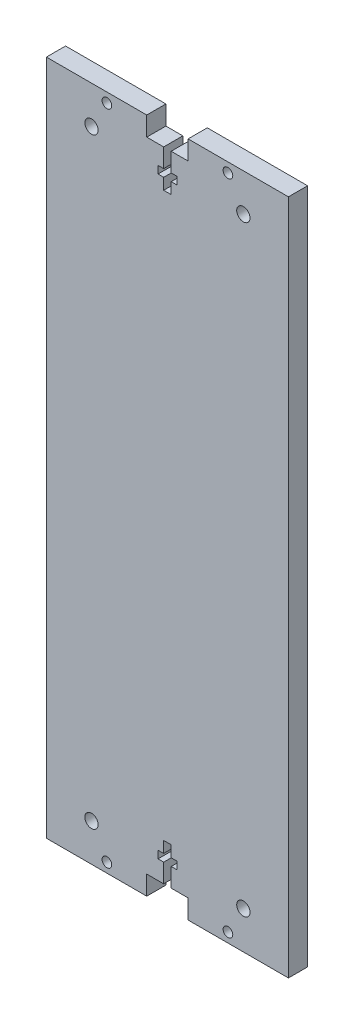
SolidWorks part; units mm, degrees
ref_plane "Front Plane" through (0, 0, 0) normal (0, 0, 1) x (1, 0, 0)
ref_plane "Top Plane" through (0, 0, 0) normal (0, 1, 0) x (1, 0, 0)
ref_plane "Right Plane" through (0, 0, 0) normal (1, 0, 0) x (0, 0, -1)
sketch "Sketch1" plane through (0, 0, 0) normal (0, 0, 1) x (1, 0, 0)
  line L0 (0, -107.823) -> (0, -114.3)
  line L1 (-40.894, -114.3) -> (40.894, -114.3)
  line L2 (-40.894, -114.3) -> (-40.894, 114.3)
  line L3 (-40.894, 114.3) -> (40.894, 114.3)
  line L4 (40.894, -114.3) -> (40.894, 114.3)
  line L5 (-40.894, -114.3) -> (40.894, 114.3) construction
  line L6 (-40.894, 114.3) -> (40.894, -114.3) construction
  line L7 (-6.985, -114.3) -> (6.985, -114.3)
  line L8 (-6.985, -114.3) -> (-6.985, -107.823)
  line L9 (-6.985, -107.823) -> (6.985, -107.823)
  line L10 (6.985, -114.3) -> (6.985, -107.823)
  line L11 (0, -95.123) -> (0, -107.823) construction
  line L12 (-1.27, -107.823) -> (1.27, -107.823)
  line L13 (-1.27, -107.823) -> (-1.27, -95.123)
  line L14 (-1.27, -95.123) -> (1.27, -95.123)
  line L15 (1.27, -107.823) -> (1.27, -95.123)
  line L16 (0, -98.933) -> (0, -101.473) construction
  line L17 (-3.175, -101.473) -> (3.175, -101.473)
  line L18 (-3.175, -101.473) -> (-3.175, -98.933)
  line L19 (-3.175, -98.933) -> (3.175, -98.933)
  line L20 (3.175, -101.473) -> (3.175, -98.933)
  line L21 (0, 0) -> (-40.894, 0) construction
  line L22 (0, 98.933) -> (0, 101.473) construction
  line L23 (0, 95.123) -> (0, 107.823) construction
  line L24 (3.175, 101.473) -> (3.175, 98.933)
  line L25 (-3.175, 98.933) -> (3.175, 98.933)
  line L26 (-3.175, 101.473) -> (-3.175, 98.933)
  line L27 (-3.175, 101.473) -> (3.175, 101.473)
  line L28 (0, 0) -> (0, 14.3328) construction
  line L29 (1.27, 107.823) -> (1.27, 95.123)
  line L30 (-1.27, 95.123) -> (1.27, 95.123)
  line L31 (-1.27, 107.823) -> (-1.27, 95.123)
  line L32 (-1.27, 107.823) -> (1.27, 107.823)
  line L33 (6.985, 114.3) -> (6.985, 107.823)
  line L34 (-6.985, 107.823) -> (6.985, 107.823)
  line L35 (-6.985, 114.3) -> (-6.985, 107.823)
  line L36 (-6.985, 114.3) -> (6.985, 114.3)
  line L37 (0, 107.823) -> (0, 114.3)
  circle A0 centre (-25.654, 101.6) radius 2.2479
  circle A1 centre (25.654, 101.6) radius 2.2479
  circle A2 centre (-20.447, -111.0615) radius 1.6319
  circle A3 centre (20.447, -111.0615) radius 1.6319
  circle A4 centre (20.447, 111.0615) radius 1.6319
  circle A5 centre (-20.447, 111.0615) radius 1.6319
  circle A6 centre (25.654, -101.6) radius 2.2479
  circle A7 centre (-25.654, -101.6) radius 2.2479
  point P0 (0, 0)
  point P24 (-20.447, -114.3)
  point P30 (20.447, -114.3)
  point P58 (20.447, 114.3)
  point P59 (-20.447, 114.3)
  dimension "D12" = 4.4958
  dimension "D15" = 3.2639
  dimension "D1" = 228.6
  dimension "D2" = 81.788
  dimension "D3" = 13.97
  dimension "D4" = 6.477
  dimension "D5" = 40.894
  dimension "D6" = 12.7
  dimension "D7" = 2.54
  dimension "D8" = 6.35
  dimension "D9" = 2.54
  dimension "D10" = 6.35
  dimension "D11" = 20.447
  dimension "D13" = 12.7
  dimension "D14" = 15.24
  dimension "D16" = 3.2385
extrude "Boss-Extrude1" add sketch "Sketch1" along normal blind 6.477 contours L10 L1 L4 L3 L2 L8 L9
